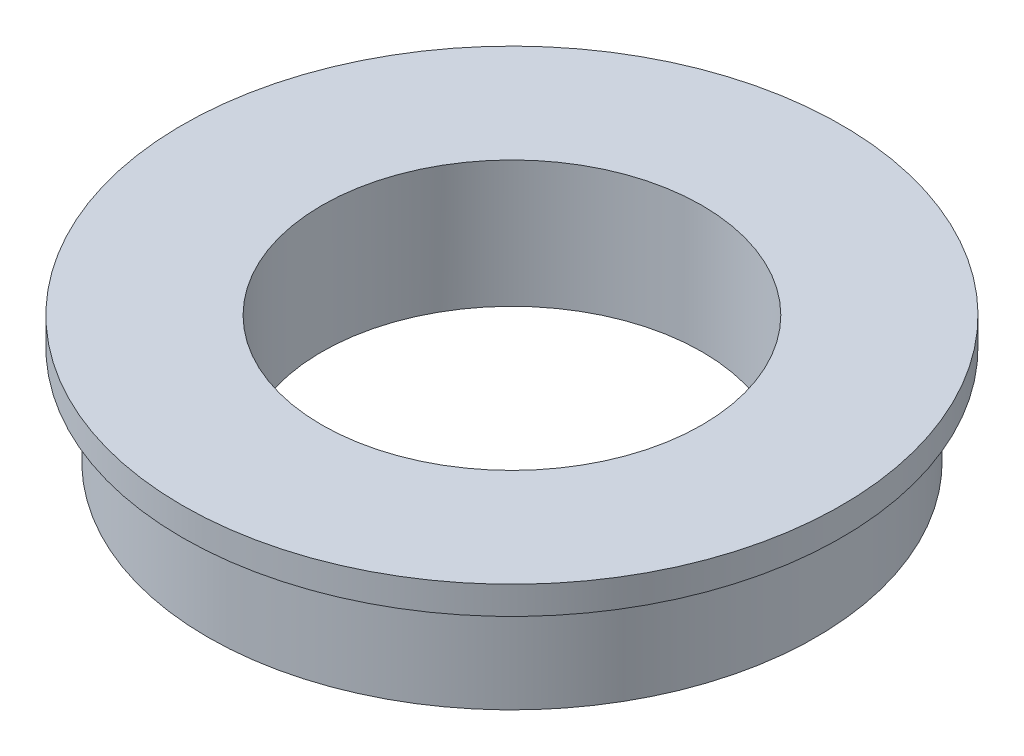
SolidWorks part; units mm, degrees
ref_plane "前视基准面" through (0, 0, 0) normal (0, 0, 1) x (1, 0, 0)
ref_plane "上视基准面" through (0, 0, 0) normal (0, 1, 0) x (1, 0, 0)
ref_plane "右视基准面" through (0, 0, 0) normal (1, 0, 0) x (0, 0, -1)
sketch "草图1" plane through (0, 0, 0) normal (0, 1, 0) x (1, 0, 0)
  circle A0 centre (0, 0) radius 12
extrude "凸台-拉伸1" add sketch "草图1" along normal blind 3.9
sketch "草图2" plane through (0, 3.9, 0) normal (0, 1, 0) x (1, 0, 0)
  circle A0 centre (0, 0) radius 13
extrude "凸台-拉伸2" add sketch "草图2" along normal blind 1.1
sketch "草图3" plane through (0, 0, 0) normal (0, -1, 0) x (1, 0, 0)
  circle A0 centre (0, 0) radius 7.5
extrude "切除-拉伸1" cut sketch "草图3" against normal up to surface (5 mm away) up to face at (0, 5, 13)
